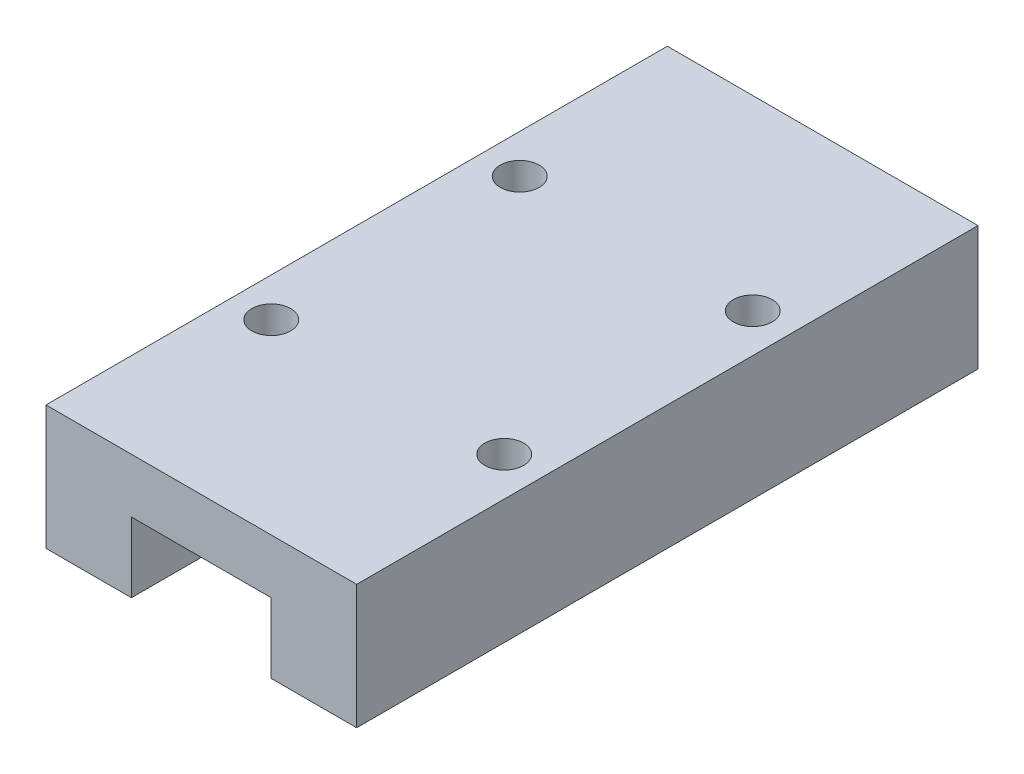
SolidWorks part; units mm, degrees
ref_plane "Front" through (0, 0, 0) normal (0, 0, 1) x (1, 0, 0)
ref_plane "Top" through (0, 0, 0) normal (0, 1, 0) x (1, 0, 0)
ref_plane "Right" through (0, 0, 0) normal (1, 0, 0) x (0, 0, -1)
sketch "Sketch2" plane through (0, 0, 0) normal (0, 0, 1) x (1, 0, 0)
  line L0 (0, 0) -> (0, 8)
  line L1 (0, 8) -> (20, 8)
  line L2 (20, 8) -> (20, 0)
  line L3 (20, 0) -> (14.5, 0)
  line L4 (14.5, 0) -> (14.5, 4.5)
  line L5 (14.5, 4.5) -> (5.5, 4.5)
  line L6 (5.5, 4.5) -> (5.5, 0)
  line L7 (5.5, 0) -> (0, 0)
  dimension "D1" = 20
  dimension "D2" = 8
  dimension "5.5" = 5.5
  dimension "D4" = 4.5
extrude "Boss-Extrude1" add sketch "Sketch2" along normal blind 40
hole_wizard "M3x0.5 Tapped Hole1" positions "Sketch3" profile "Sketch4" tap size "M3x0.5" standard "ANSI Metric"
sketch "Sketch3" plane through (0, 8, 0) normal (0, 1, 0) x (1, 0, 0)
  line L0 (0, -20) -> (20, -20) construction
  line L1 (0, -40) -> (0, 0) construction
  line L2 (20, -40) -> (20, 0) construction
  line L5 (10, 0) -> (10, -40) construction
  line L6 (20, 0) -> (0, 0) construction
  line L7 (20, -40) -> (0, -40) construction
  line L10 (17.5, -28) -> (2.5, -28)
  line L11 (17.5, -28) -> (17.5, -12)
  line L12 (17.5, -12) -> (2.5, -12)
  line L13 (2.5, -28) -> (2.5, -12)
  line L14 (17.5, -28) -> (2.5, -12) construction
  line L15 (17.5, -12) -> (2.5, -28) construction
  point P35 (2.5, -12)
  point P38 (17.5, -28)
  point P39 (17.5, -12)
  point P40 (2.5, -28)
  point P78 (10, -12)
  point P79 (2.5, -20)
  dimension "D1" = 15
  dimension "D2" = 16
cosmetic thread "Hole Thread1"
cosmetic thread "Hole Thread3"
cosmetic thread "Hole Thread4"
sketch "Sketch4" plane through (2.5, 8, 28) normal (1, 0, 0) x (0, 0, 1)
  line L0 (0, 0) -> (0, 6.7511)
  line L1 (0, 6.7511) -> (1.25, 6)
  line L2 (1.25, 6) -> (1.25, 0)
  line L5 (1.25, 0) -> (0, 0)
  line L10 (0, 6.7511) -> (-1.25, 6) construction
  line L11 (0, -6.35) -> (0, 107.95) construction
  dimension "Tap Drill Dia." = 2.5
  dimension "Tap Drill Depth" = 6
  dimension "Drill Angle" = 118
cosmetic thread "Hole Thread5"
